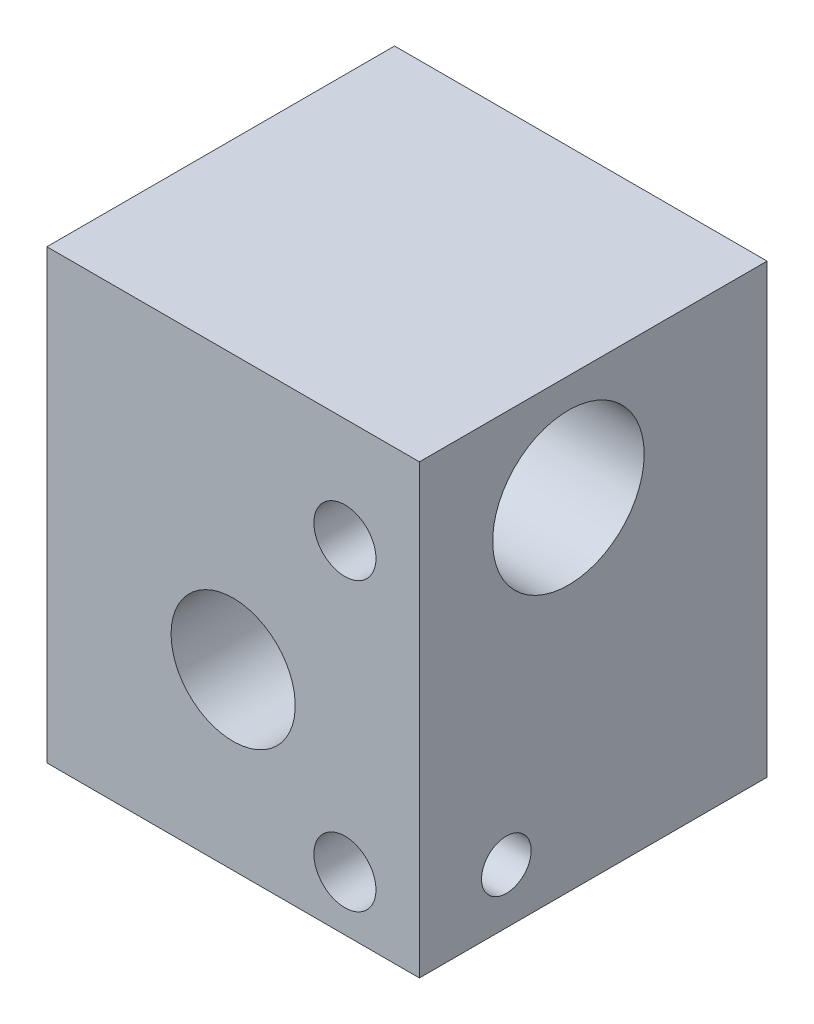
SolidWorks part; units mm, degrees
material "aluminio"
ref_plane "Front Plane" through (0, 0, 0) normal (0, 0, 1) x (1, 0, 0)
ref_plane "Top Plane" through (0, 0, 0) normal (0, 1, 0) x (1, 0, 0)
ref_plane "Right Plane" through (0, 0, 0) normal (1, 0, 0) x (0, 0, -1)
sketch "Sketch1" plane through (0, 0, 0) normal (0, 0, 1) x (1, 0, 0)
  line L1 (-7.5, -9) -> (7.5, -9)
  line L2 (-7.5, -9) -> (-7.5, 9)
  line L3 (-7.5, 9) -> (7.5, 9)
  line L4 (7.5, -9) -> (7.5, 9)
  line L5 (-7.5, -9) -> (7.5, 9) construction
  line L6 (-7.5, 9) -> (7.5, -9) construction
  point P0 (0, 0)
  dimension "D1" = 18
  dimension "D2" = 15
extrude "Boss-Extrude1" add sketch "Sketch1" along normal blind 14
sketch "Sketch2" plane through (0, 0, 0) normal (0, 0, -1) x (-1, 0, 0)
  line L0 (0, 9) -> (0, -9) construction
  line L1 (7.5, -9) -> (-7.5, -9) construction
  line L2 (-7.5, 9) -> (7.5, 9) construction
  circle A0 centre (0, -2) radius 2.5
  dimension "D1" = 5
  dimension "D2" = 7
extrude "Cut-Extrude1" cut sketch "Sketch2" against normal through all
cosmetic thread "Rosca cosmética1" parameters "D2"=6
sketch "Sketch3" plane through (7.5, 0, 0) normal (1, 0, 0) x (0, 0, -1)
  line L0 (-14, 0) -> (0, 0) construction
  line L1 (-14, -9) -> (-14, 9) construction
  line L2 (0, -9) -> (0, 9) construction
  line L3 (-8, 0) -> (-8, 9) construction
  line L5 (-14, 9) -> (0, 9) construction
  circle A0 centre (-8, 4.75) radius 3.05
  dimension "D1" = 6.1
  dimension "D3" = 6
  dimension "D2" = 1.2
extrude "Cut-Extrude2" cut sketch "Sketch3" against normal through all
sketch "Sketch4" plane through (7.5, 0, 0) normal (1, 0, 0) x (0, 0, -1)
  line L0 (0, -6.8) -> (-14, -6.8) construction
  line L3 (-10.5, -6.8) -> (-10.5, -9) construction
  line L4 (-14, -9) -> (0, -9) construction
  line L5 (0, -9) -> (0, 9) construction
  line L6 (-14, -9) -> (-14, 9) construction
  circle A0 centre (-10.5, -6.8) radius 0.9
  dimension "D1" = 1.8
  dimension "D2" = 2.2
  dimension "D3" = 3.5
hole_wizard "Taladro roscado M31" positions "Croquis3" profile "Croquis2" tap size "M3" standard "Iso"
sketch "Croquis3" plane through (-2.6487, -2.9752, 14) normal (0, 0, -1) x (1, 0, 0)
  line L3 (10.1487, -7.7252) -> (-4.8513, -7.7252) construction
  line L4 (10.1487, 6.0248) -> (10.1487, -11.9752) construction
  line L5 (-4.8513, -11.9752) -> (-4.8513, 6.0248) construction
  line L7 (10.1487, -10.7752) -> (10.1487, -4.6752) construction
  line L8 (10.1487, 3.8248) -> (-4.8513, 3.8248) construction
  point P0 (7.1487, -7.7252)
  point P28 (7.1487, 3.8248)
  dimension "D1" = 3
  dimension "D2" = 3
cosmetic thread "Rosca de taladro1" parameters "D1"=3.2179, "D2"=3
cosmetic thread "Rosca de taladro4" parameters "D1"=4, "D2"=3
sketch "Croquis2" plane through (4.5, 4.75, 14) normal (1, 0, 0) x (0, -1, 0)
  line L0 (0, 0) -> (0, 4.7511)
  line L1 (0, 4.7511) -> (1.25, 4)
  line L2 (1.25, 4) -> (1.25, 0)
  line L5 (1.25, 0) -> (0, 0)
  line L10 (0, 4.7511) -> (-1.25, 4) construction
  line L11 (0, -6.35) -> (0, 107.95) construction
  dimension "Diámetro de perforador para roscar" = 2.5
  dimension "Profundidad de perforador para roscar" = 4
  dimension "Ángulo de perforador" = 118
sketch "Croquis8" plane through (0, 0, 14) normal (0, 0, 1) x (1, 0, 0)
  line L1 (7.5, 4.75) -> (-7.5, 4.75) construction
  line L2 (7.5, -9) -> (7.5, 9) construction
  line L3 (-7.5, 9) -> (-7.5, -9) construction
  line L4 (7.5, 1.7) -> (7.5, 7.8) construction
  line L5 (-7.5, 7.8) -> (-7.5, 1.7) construction
  point P0 (0, 4.75)
hole_wizard "Diámetro de taladro Ø2.8 (2.8)1" positions "Croquis3D1" profile "Croquis11" hole size "Ø2.8" standard "Iso"
sketch3d "Croquis3D1"
  point P0 (7.5, -6.8, 10.5)
sketch "Croquis11" plane through (7.5, -6.8, 10.5) normal (0, 1, 0) x (0, 0, -1)
  line L0 (0, 0) -> (0, 12.6009)
  line L1 (0, 12.6009) -> (1, 12)
  line L2 (1, 12) -> (1, 0)
  line L5 (1, 0) -> (0, 0)
  line L10 (0, 12.6009) -> (-1, 12) construction
  line L11 (0, -6.35) -> (0, 107.95) construction
  dimension "Diámetro de taladro" = 2
  dimension "Profundidad de taladro" = 12
  dimension "Ángulo de perforador" = 118
